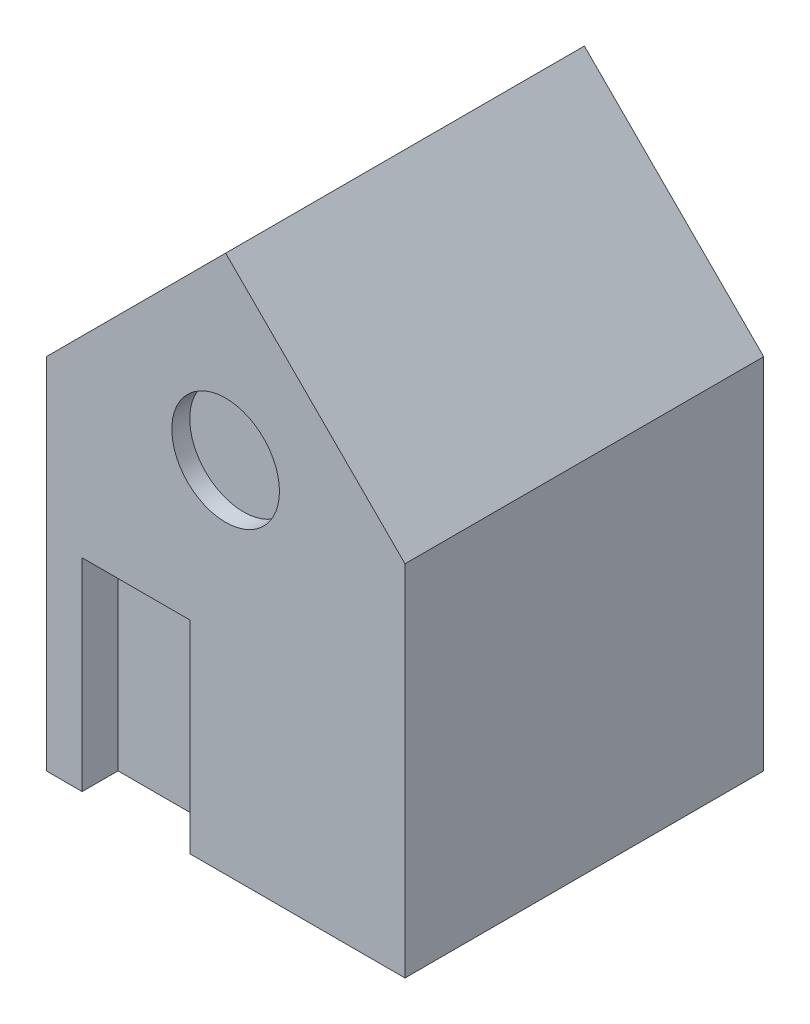
SolidWorks part; units mm, degrees
ref_plane "Front Plane" through (0, 0, 0) normal (0, 0, 1) x (1, 0, 0)
ref_plane "Top Plane" through (0, 0, 0) normal (0, 1, 0) x (1, 0, 0)
ref_plane "Right Plane" through (0, 0, 0) normal (1, 0, 0) x (0, 0, -1)
sketch "Sketch1" plane through (0, 0, 0) normal (0, 0, 1) x (1, 0, 0)
  line L0 (-50, 0) -> (50, 0)
  line L1 (50, 0) -> (50, 100)
  line L2 (50, 100) -> (0, 150)
  line L3 (0, 150) -> (-50, 100)
  line L4 (-50, 100) -> (-50, 0)
  dimension "D1" = 100
  dimension "D2" = 100
  dimension "D3" = 90
extrude "Boss-Extrude1" add sketch "Sketch1" along normal mid plane 100
sketch "Sketch2" plane through (0, 0, 50) normal (0, 0, 1) x (1, 0, 0)
  line L0 (-50, 0) -> (50, 0) construction
  line L1 (-40, 0) -> (-10, 0)
  line L2 (-40, 0) -> (-40, 56.4513)
  line L3 (-40, 56.4513) -> (-10, 56.4513)
  line L4 (-10, 0) -> (-10, 56.4513)
  line L5 (-25, 56.4513) -> (-25, 0) construction
  line L6 (-40, 28.2257) -> (-10, 28.2257) construction
  point P368 (-25, 28.2257)
  dimension "D1" = 30
  dimension "D2" = 56.4513
  dimension "D3" = 10
extrude "Cut-Extrude1" cut sketch "Sketch2" against normal blind 10
sketch "Sketch3" plane through (0, 0, 50) normal (0, 0, 1) x (1, 0, 0)
  circle A0 centre (0, 100) radius 15
  point P2 (0, 0)
  point P4 (0, 0)
  point P5 (0, 0)
  dimension "D1" = 30
  dimension "D2" = 100
extrude "Cut-Extrude2" cut sketch "Sketch3" against normal blind 5
sketch "Sketch4" plane through (0, 0, 0) normal (0, 0, 1) x (1, 0, 0)
  line L0 (-50, 100) -> (0, 150)
  line L1 (0, 150) -> (50, 100)
  line L2 (50, 100) -> (53.5355, 103.5355)
  line L3 (53.5355, 103.5355) -> (0, 157.0711)
  line L4 (0, 157.0711) -> (-53.4959, 103.5752)
  line L5 (-53.4959, 103.5752) -> (-49.9604, 100.0396)
  line L6 (-49.9604, 100.0396) -> (0, 150)
  point P4 (0, 159.508)
  point P11 (0, 0)
  point P12 (0, 0)
  point P13 (0, 0)
  point P14 (0, 0)
  point P15 (0, 0)
  point P16 (0, 0)
  point P17 (0, 0)
  point P18 (-53.4959, 103.5355)
  dimension "D1" = 5
